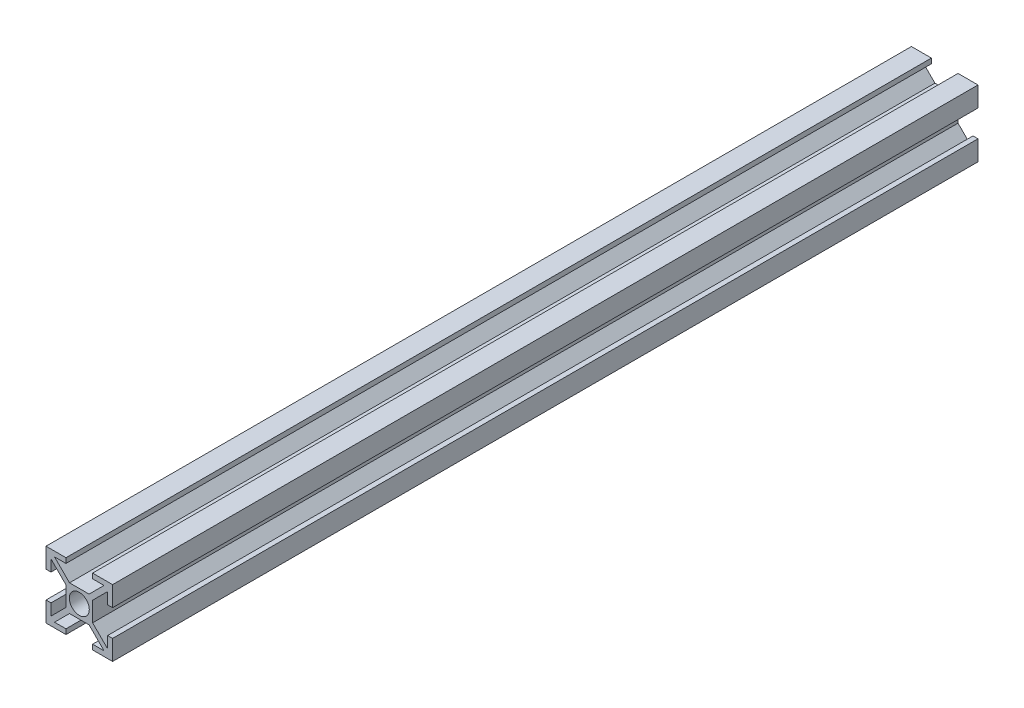
SolidWorks part; units mm, degrees
material "3.0205 (EN-AW 1200)"
ref_plane "Plano frontal" through (0, 0, 0) normal (0, 0, 1) x (1, 0, 0)
ref_plane "Plano superior" through (0, 0, 0) normal (0, 1, 0) x (1, 0, 0)
ref_plane "Plano direito" through (0, 0, 0) normal (1, 0, 0) x (0, 0, -1)
sketch "Esboço1" plane through (0, 0, 0) normal (0, 0, 1) x (1, 0, 0)
  line L0 (-2.9393, 4) -> (2.9393, 4)
  line L1 (-10, -10) -> (-4, -10)
  line L2 (-10, -10) -> (-10, -4)
  line L3 (-10, 10) -> (-4, 10)
  line L4 (10, -10) -> (10, -4)
  line L5 (-10, -10) -> (-4, -4) construction
  line L6 (-10, 10) -> (0, 0) construction
  line L7 (-7.4393, -8.5) -> (-2.9393, -4)
  line L8 (4, -10) -> (10, -10)
  line L9 (-8.5, -7.4393) -> (-4, -2.9393)
  line L10 (-8.5, 7.4393) -> (-4, 2.9393)
  line L11 (-7.4393, -8.5) -> (-4, -8.5)
  line L12 (-8.5, -7.4393) -> (-8.5, -4)
  line L13 (-7.4393, 8.5) -> (-4, 8.5)
  line L14 (8.5, -7.4393) -> (8.5, -4)
  line L17 (-4, 10) -> (-4, 8.5)
  line L18 (4, -8.5) -> (7.4393, -8.5)
  line L19 (-10, -4) -> (-8.5, -4)
  line L20 (4, 10) -> (4, 8.5)
  line L21 (-10, 4) -> (-8.5, 4)
  line L22 (-4, 2.9393) -> (-4, -2.9393)
  line L23 (-4, -8.5) -> (-4, -10)
  line L24 (-8.5, 4) -> (-8.5, 7.4393)
  line L25 (-10, 4) -> (-10, 10)
  line L26 (-7.4393, 8.5) -> (-2.9393, 4)
  line L27 (4, 8.5) -> (7.4393, 8.5)
  line L28 (-2.9393, -4) -> (2.9393, -4)
  line L29 (4, 10) -> (10, 10)
  line L30 (4, -8.5) -> (4, -10)
  line L31 (10, 4) -> (10, 10)
  line L32 (8.5, 4) -> (8.5, 7.4393)
  line L33 (-10.5303, -9.4697) -> (9.4697, 10.5303) construction
  line L34 (8.5, 4) -> (10, 4)
  line L35 (8.5, -4) -> (10, -4)
  line L36 (-10, -10) -> (10, 10) construction
  line L37 (4, 2.9393) -> (4, -2.9393)
  line L38 (-9.4697, -10.5303) -> (10.5303, 9.4697) construction
  line L40 (2.9393, -4) -> (7.4393, -8.5)
  line L41 (4, -4) -> (10, -10) construction
  line L43 (4, -2.9393) -> (8.5, -7.4393)
  line L44 (4, 0) -> (10, 0) construction
  line L45 (4, 2.9393) -> (8.5, 7.4393)
  line L47 (4, 4) -> (10, 10) construction
  line L48 (2.9393, 4) -> (7.4393, 8.5)
  circle A0 centre (0, 0) radius 3
  point P0 (0, 0)
  point P14 (-4.0323, -3.9672)
  dimension "D5" = 6
  dimension "D1" = 0.75
  dimension "D3" = 1.5
  dimension "D4" = 20
  dimension "D6" = 8
  dimension "D7" = 20
  dimension "D9" = 1.5
  dimension "D2" = 8
extrude "Ressalto-extrusão1" add sketch "Esboço1" along normal blind 260
